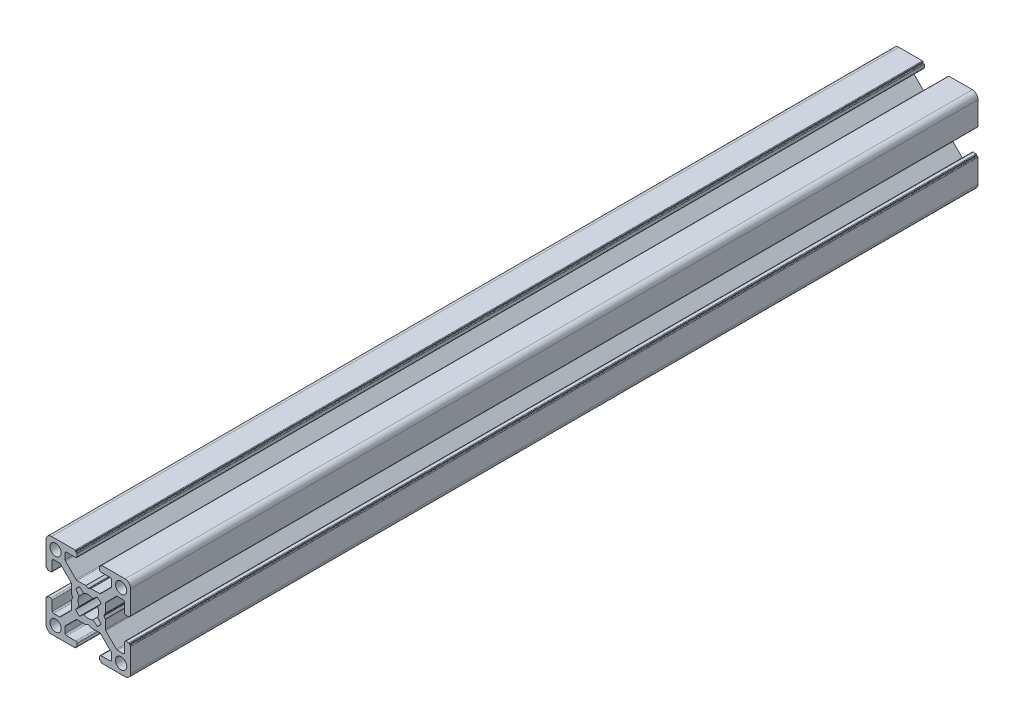
SolidWorks part; units mm, degrees
ref_plane "Alzado" through (0, 0, 0) normal (0, 0, 1) x (1, 0, 0)
ref_plane "Planta" through (0, 0, 0) normal (0, 1, 0) x (1, 0, 0)
ref_plane "Vista lateral" through (0, 0, 0) normal (1, 0, 0) x (0, 0, -1)
ref_plane "Plano1" through (0, 0, 1000) normal (0, 0, 1) x (1, 0, 0)
sketch "Croquis1" plane through (0, 0, 1000) normal (0, 0, 1) x (1, 0, 0)
  line L16 (-7.8359, -10.4816) -> (-6.3001, -11.7194)
  line L17 (-3.0999, -11.7194) -> (-1.5641, -10.4816)
  line L18 (-0.1947, -11.8453) -> (-1.4194, -13.3999)
  line L19 (-1.4194, -16.6001) -> (-0.1947, -18.1547)
  line L20 (-1.5641, -19.5184) -> (-3.0999, -18.2806)
  line L21 (-6.3001, -18.2806) -> (-7.8359, -19.5184)
  line L22 (-9.2053, -18.1547) -> (-7.9806, -16.6001)
  line L23 (-7.9806, -13.3999) -> (-9.2053, -11.8453)
  line L24 (9.8, -10.5) -> (10.1, -10.5)
  line L25 (10.3, -10.3) -> (10.3, -2)
  line L26 (8.3, 0) -> (0, 0)
  line L27 (-0.2, -0.2) -> (-0.2, -0.5)
  line L28 (-0.2, -0.5) -> (-0.5, -0.5)
  line L29 (-0.7, -0.7) -> (-0.7, -1.7)
  line L30 (-0.2, -2.2) -> (3.05, -2.2)
  line L31 (3.55, -2.7) -> (3.55, -4.7431)
  line L32 (3.4037, -5.0964) -> (-0.3491, -8.8534)
  line L33 (-0.7028, -9) -> (-3.7468, -9)
  line L34 (-3.8462, -9.0264) -> (-4.6006, -9.4583)
  line L35 (-4.7994, -9.4583) -> (-5.5538, -9.0264)
  line L36 (-5.6532, -9) -> (-8.6972, -9)
  line L37 (-9.0509, -8.8534) -> (-12.8037, -5.0964)
  line L38 (-12.95, -4.7431) -> (-12.95, -2.7)
  line L39 (-12.45, -2.2) -> (-9.2, -2.2)
  line L40 (-8.7, -1.7) -> (-8.7, -0.7)
  line L41 (-8.9, -0.5) -> (-9.2, -0.5)
  line L42 (-9.2, -0.5) -> (-9.2, -0.2)
  line L43 (-9.4, 0) -> (-17.7, 0)
  line L44 (-19.7, -2) -> (-19.7, -10.3)
  line L45 (-19.5, -10.5) -> (-19.2, -10.5)
  line L46 (-19.2, -10.5) -> (-19.2, -10.8)
  line L47 (-19, -11) -> (-18, -11)
  line L48 (-17.5, -10.5) -> (-17.5, -7.25)
  line L49 (-17, -6.75) -> (-14.9569, -6.75)
  line L50 (-14.6036, -6.8963) -> (-10.8466, -10.6491)
  line L51 (-10.7, -11.0028) -> (-10.7, -14.0468)
  line L52 (-10.6736, -14.1462) -> (-10.2417, -14.9006)
  line L53 (-10.2417, -15.0994) -> (-10.6736, -15.8538)
  line L54 (-10.7, -15.9532) -> (-10.7, -18.9972)
  line L55 (-10.8466, -19.3509) -> (-14.6036, -23.1037)
  line L56 (-14.9569, -23.25) -> (-17, -23.25)
  line L57 (-17.5, -22.75) -> (-17.5, -19.5)
  line L58 (-18, -19) -> (-19, -19)
  line L59 (-19.2, -19.2) -> (-19.2, -19.5)
  line L60 (-19.2, -19.5) -> (-19.5, -19.5)
  line L61 (-19.7, -19.7) -> (-19.7, -28)
  line L62 (-17.7, -30) -> (-9.4, -30)
  line L63 (-9.2, -29.8) -> (-9.2, -29.5)
  line L64 (-9.2, -29.5) -> (-8.9, -29.5)
  line L65 (-8.7, -29.3) -> (-8.7, -28.3)
  line L66 (-9.2, -27.8) -> (-12.45, -27.8)
  line L67 (-12.95, -27.3) -> (-12.95, -25.2569)
  line L68 (-12.8037, -24.9036) -> (-9.0509, -21.1466)
  line L69 (-8.6972, -21) -> (-5.6532, -21)
  line L70 (-5.5538, -20.9736) -> (-4.7994, -20.5417)
  line L71 (-4.6006, -20.5417) -> (-3.8462, -20.9736)
  line L72 (-3.7468, -21) -> (-0.7028, -21)
  line L73 (-0.3491, -21.1466) -> (3.4037, -24.9036)
  line L74 (3.55, -25.2569) -> (3.55, -27.3)
  line L75 (3.05, -27.8) -> (-0.2, -27.8)
  line L76 (-0.7, -28.3) -> (-0.7, -29.3)
  line L77 (-0.5, -29.5) -> (-0.2, -29.5)
  line L78 (-0.2, -29.5) -> (-0.2, -29.8)
  line L79 (0, -30) -> (8.3, -30)
  line L80 (10.3, -28) -> (10.3, -19.7)
  line L81 (10.1, -19.5) -> (9.8, -19.5)
  line L82 (9.8, -19.5) -> (9.8, -19.2)
  line L83 (9.6, -19) -> (8.6, -19)
  line L84 (8.1, -19.5) -> (8.1, -22.75)
  line L85 (7.6, -23.25) -> (5.5569, -23.25)
  line L86 (5.2036, -23.1037) -> (1.4466, -19.3509)
  line L87 (1.3, -18.9972) -> (1.3, -15.9532)
  line L88 (1.2736, -15.8538) -> (0.8417, -15.0994)
  line L89 (0.8417, -14.9006) -> (1.2736, -14.1462)
  line L90 (1.3, -14.0468) -> (1.3, -11.0028)
  line L91 (1.4466, -10.6491) -> (5.2036, -6.8963)
  line L92 (5.5569, -6.75) -> (7.6, -6.75)
  line L93 (8.1, -7.25) -> (8.1, -10.5)
  line L94 (8.6, -11) -> (9.6, -11)
  line L95 (9.8, -10.8) -> (9.8, -10.5)
  line L96 (8, -2.3) -> (5.8, -4.5) construction
  line L97 (-15.2, -2.3) -> (-17.4, -4.5) construction
  line L98 (-4.7, -15) -> (6.9, -15) construction
  arc A16 (-9.2053, -11.8453) -> (-7.8359, -10.4816) centre (-4.7, -15) cw
  arc A17 (-6.3001, -11.7194) -> (-3.0999, -11.7194) centre (-4.7, -15) cw
  arc A18 (-1.5641, -10.4816) -> (-0.1947, -11.8453) centre (-4.7, -15) cw
  arc A19 (-1.4194, -13.3999) -> (-1.4194, -16.6001) centre (-4.7, -15) cw
  arc A20 (-0.1947, -18.1547) -> (-1.5641, -19.5184) centre (-4.7, -15) cw
  arc A21 (-3.0999, -18.2806) -> (-6.3001, -18.2806) centre (-4.7, -15) cw
  arc A22 (-7.8359, -19.5184) -> (-9.2053, -18.1547) centre (-4.7, -15) cw
  arc A23 (-7.9806, -16.6001) -> (-7.9806, -13.3999) centre (-4.7, -15) cw
  arc A24 (10.1, -10.5) -> (10.3, -10.3) centre (10.1, -10.3) ccw
  arc A25 (10.3, -2) -> (8.3, 0) centre (8.3, -2) ccw
  arc A26 (0, 0) -> (-0.2, -0.2) centre (0, -0.2) ccw
  arc A27 (-0.5, -0.5) -> (-0.7, -0.7) centre (-0.5, -0.7) ccw
  arc A28 (-0.7, -1.7) -> (-0.2, -2.2) centre (-0.2, -1.7) ccw
  arc A29 (3.05, -2.2) -> (3.55, -2.7) centre (3.05, -2.7) cw
  arc A30 (3.55, -4.7431) -> (3.4037, -5.0964) centre (3.05, -4.7431) cw
  arc A31 (-0.3491, -8.8534) -> (-0.7028, -9) centre (-0.7028, -8.5) cw
  arc A32 (-3.7468, -9) -> (-3.8462, -9.0264) centre (-3.7468, -9.2) ccw
  arc A33 (-4.6006, -9.4583) -> (-4.7994, -9.4583) centre (-4.7, -9.2847) cw
  arc A34 (-5.5538, -9.0264) -> (-5.6532, -9) centre (-5.6532, -9.2) ccw
  arc A35 (-8.6972, -9) -> (-9.0509, -8.8534) centre (-8.6972, -8.5) cw
  arc A36 (-12.8037, -5.0964) -> (-12.95, -4.7431) centre (-12.45, -4.7431) cw
  arc A37 (-12.95, -2.7) -> (-12.45, -2.2) centre (-12.45, -2.7) cw
  arc A38 (-9.2, -2.2) -> (-8.7, -1.7) centre (-9.2, -1.7) ccw
  arc A39 (-8.7, -0.7) -> (-8.9, -0.5) centre (-8.9, -0.7) ccw
  arc A40 (-9.2, -0.2) -> (-9.4, 0) centre (-9.4, -0.2) ccw
  arc A41 (-17.7, 0) -> (-19.7, -2) centre (-17.7, -2) ccw
  arc A42 (-19.7, -10.3) -> (-19.5, -10.5) centre (-19.5, -10.3) ccw
  arc A43 (-19.2, -10.8) -> (-19, -11) centre (-19, -10.8) ccw
  arc A44 (-18, -11) -> (-17.5, -10.5) centre (-18, -10.5) ccw
  arc A45 (-17.5, -7.25) -> (-17, -6.75) centre (-17, -7.25) cw
  arc A46 (-14.9569, -6.75) -> (-14.6036, -6.8963) centre (-14.9569, -7.25) cw
  arc A47 (-10.8466, -10.6491) -> (-10.7, -11.0028) centre (-11.2, -11.0028) cw
  arc A48 (-10.7, -14.0468) -> (-10.6736, -14.1462) centre (-10.5, -14.0468) ccw
  arc A49 (-10.2417, -14.9006) -> (-10.2417, -15.0994) centre (-10.4153, -15) cw
  arc A50 (-10.6736, -15.8538) -> (-10.7, -15.9532) centre (-10.5, -15.9532) ccw
  arc A51 (-10.7, -18.9972) -> (-10.8466, -19.3509) centre (-11.2, -18.9972) cw
  arc A52 (-14.6036, -23.1037) -> (-14.9569, -23.25) centre (-14.9569, -22.75) cw
  arc A53 (-17, -23.25) -> (-17.5, -22.75) centre (-17, -22.75) cw
  arc A54 (-17.5, -19.5) -> (-18, -19) centre (-18, -19.5) ccw
  arc A55 (-19, -19) -> (-19.2, -19.2) centre (-19, -19.2) ccw
  arc A56 (-19.5, -19.5) -> (-19.7, -19.7) centre (-19.5, -19.7) ccw
  arc A57 (-19.7, -28) -> (-17.7, -30) centre (-17.7, -28) ccw
  arc A58 (-9.4, -30) -> (-9.2, -29.8) centre (-9.4, -29.8) ccw
  arc A59 (-8.9, -29.5) -> (-8.7, -29.3) centre (-8.9, -29.3) ccw
  arc A60 (-8.7, -28.3) -> (-9.2, -27.8) centre (-9.2, -28.3) ccw
  arc A61 (-12.45, -27.8) -> (-12.95, -27.3) centre (-12.45, -27.3) cw
  arc A62 (-12.95, -25.2569) -> (-12.8037, -24.9036) centre (-12.45, -25.2569) cw
  arc A63 (-9.0509, -21.1466) -> (-8.6972, -21) centre (-8.6972, -21.5) cw
  arc A64 (-5.6532, -21) -> (-5.5538, -20.9736) centre (-5.6532, -20.8) ccw
  arc A65 (-4.7994, -20.5417) -> (-4.6006, -20.5417) centre (-4.7, -20.7153) cw
  arc A66 (-3.8462, -20.9736) -> (-3.7468, -21) centre (-3.7468, -20.8) ccw
  arc A67 (-0.7028, -21) -> (-0.3491, -21.1466) centre (-0.7028, -21.5) cw
  arc A68 (3.4037, -24.9036) -> (3.55, -25.2569) centre (3.05, -25.2569) cw
  arc A69 (3.55, -27.3) -> (3.05, -27.8) centre (3.05, -27.3) cw
  arc A70 (-0.2, -27.8) -> (-0.7, -28.3) centre (-0.2, -28.3) ccw
  arc A71 (-0.7, -29.3) -> (-0.5, -29.5) centre (-0.5, -29.3) ccw
  arc A72 (-0.2, -29.8) -> (0, -30) centre (0, -29.8) ccw
  arc A73 (8.3, -30) -> (10.3, -28) centre (8.3, -28) ccw
  arc A74 (10.3, -19.7) -> (10.1, -19.5) centre (10.1, -19.7) ccw
  arc A75 (9.8, -19.2) -> (9.6, -19) centre (9.6, -19.2) ccw
  arc A76 (8.6, -19) -> (8.1, -19.5) centre (8.6, -19.5) ccw
  arc A77 (8.1, -22.75) -> (7.6, -23.25) centre (7.6, -22.75) cw
  arc A78 (5.5569, -23.25) -> (5.2036, -23.1037) centre (5.5569, -22.75) cw
  arc A79 (1.4466, -19.3509) -> (1.3, -18.9972) centre (1.8, -18.9972) cw
  arc A80 (1.3, -15.9532) -> (1.2736, -15.8538) centre (1.1, -15.9532) ccw
  arc A81 (0.8417, -15.0994) -> (0.8417, -14.9006) centre (1.0153, -15) cw
  arc A82 (1.2736, -14.1462) -> (1.3, -14.0468) centre (1.1, -14.0468) ccw
  arc A83 (1.3, -11.0028) -> (1.4466, -10.6491) centre (1.8, -11.0028) cw
  arc A84 (5.2036, -6.8963) -> (5.5569, -6.75) centre (5.5569, -7.25) cw
  arc A85 (7.6, -6.75) -> (8.1, -7.25) centre (7.6, -7.25) cw
  arc A86 (8.1, -10.5) -> (8.6, -11) centre (8.6, -10.5) ccw
  arc A87 (9.6, -11) -> (9.8, -10.8) centre (9.6, -10.8) ccw
  circle A88 centre (-16.3, -3.4) radius 2
  circle A89 centre (6.9, -3.4) radius 2
  circle A90 centre (-16.3, -26.6) radius 2
  circle A91 centre (6.9, -26.6) radius 2
  dimension "D3" = 4
  dimension "D1" = 30
  dimension "D2" = 30
  dimension "D4" = 23.2
  dimension "D5" = 23.2
extrude "Saliente-Extruir1" add sketch "Croquis1" against normal blind 300
